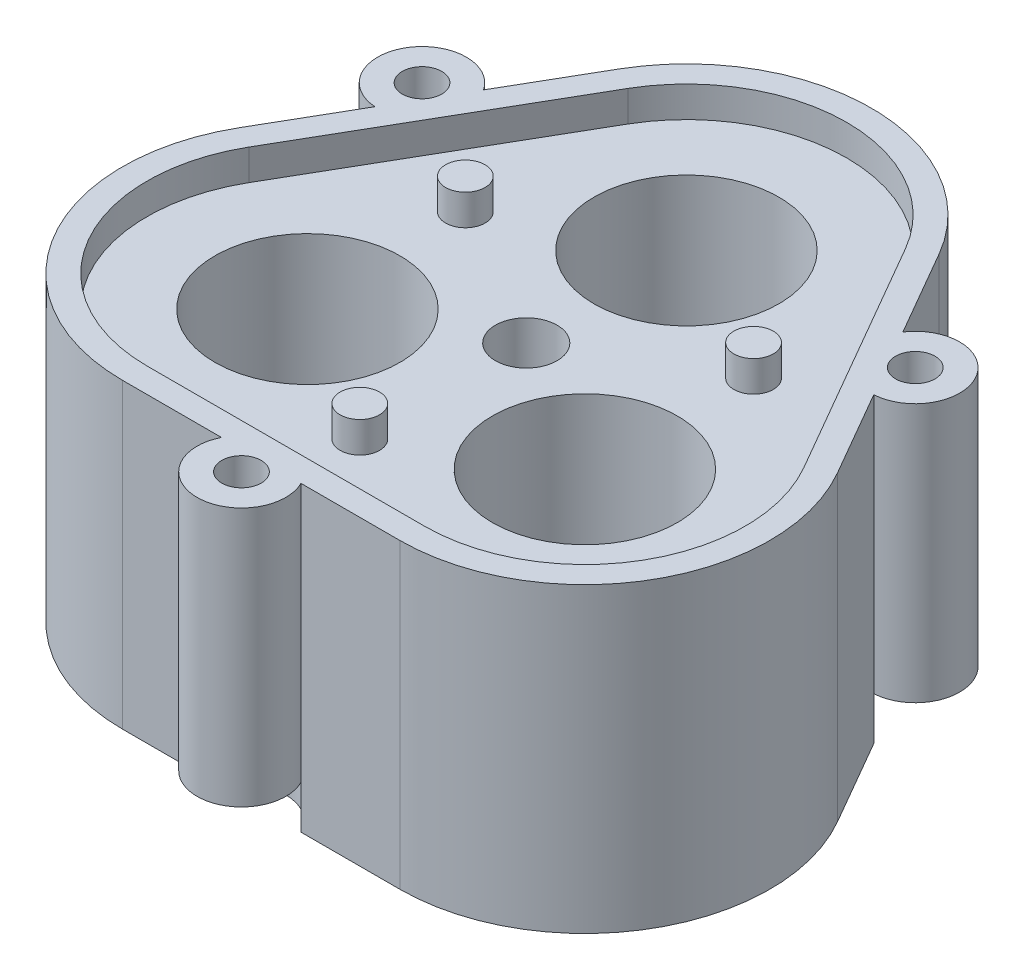
SolidWorks part; units mm, degrees
ref_plane "Front Plane" through (0, 0, 0) normal (0, 0, 1) x (1, 0, 0)
ref_plane "Top Plane" through (0, 0, 0) normal (0, 1, 0) x (1, 0, 0)
ref_plane "Right Plane" through (0, 0, 0) normal (1, 0, 0) x (0, 0, -1)
sketch "Sketch2" plane through (0, 0, 0) normal (0, 1, 0) x (1, 0, 0)
  line L0 (0, 0) -> (0, 12.9904) construction
  line L1 (0, 0) -> (11.25, -6.4952) construction
  line L2 (0, 0) -> (-11.25, -6.4952) construction
  line L3 (0, 12.9904) -> (-11.25, -6.4952) construction
  line L4 (-11.25, -6.4952) -> (11.25, -6.4952) construction
  line L5 (-11.25, -13.9952) -> (11.25, -13.9952) construction
  line L6 (6.4952, 16.7404) -> (17.7452, -2.7452) construction
  line L7 (-6.4952, 16.7404) -> (-17.7452, -2.7452) construction
  line L8 (-37.2308, -21.4952) -> (37.2308, -21.4952)
  line L9 (0, 42.9904) -> (-37.2308, -21.4952)
  line L10 (0, 42.9904) -> (37.2308, -21.4952)
  circle A0 centre (0, 12.9904) radius 7.5
  circle A1 centre (-11.25, -6.4952) radius 7.5
  circle A2 centre (11.25, -6.4952) radius 7.5
  circle A3 centre (0, 0) radius 2.5
  circle A4 centre (-11.25, -6.4952) radius 15 construction
  dimension "D3" = 15
  dimension "D9" = 5
  dimension "D10" = 30
  dimension "D1" = 120
  dimension "D2" = 120
  dimension "D4" = 22.5
  dimension "D5" = 7.5
  dimension "D6" = 7.5
  dimension "D7" = 7.5
  dimension "D8" = 74.4615
extrude "Boss-Extrude1" add sketch "Sketch2" along normal blind 12
sketch "Sketch4" plane through (0, 0, 0) normal (0, -1, 0) x (1, 0, 0)
  line L0 (-37.2308, 21.4952) -> (37.2308, 21.4952)
  line L1 (37.2308, 21.4952) -> (0, -42.9904)
  line L2 (0, -42.9904) -> (-37.2308, 21.4952)
  circle A0 centre (-11.25, 6.4952) radius 6
  circle A1 centre (11.25, 6.4952) radius 6
  circle A2 centre (0, -12.9904) radius 6
  circle A3 centre (0, 0) radius 2.5
  dimension "D1" = 12
  dimension "D2" = 5
extrude "Boss-Extrude2" add sketch "Sketch4" along normal blind 8
ref_plane "Plane1" through (0, -8, 0) normal (0, 1, 0) x (1, 0, 0)
sketch "Sketch7" plane through (0, -8, 0) normal (0, 1, 0) x (1, 0, 0)
  circle A0 centre (0, 12.9904) radius 4
  circle A1 centre (-11.25, -6.4952) radius 4
  circle A2 centre (11.25, -6.4952) radius 4
  dimension "D1" = 8
extrude "Boss-Extrude3" add sketch "Sketch7" along normal blind 8 separate body
sketch "Sketch9" plane through (0, -8, 0) normal (0, 1, 0) x (1, 0, 0)
  line L0 (0, 42.9904) -> (-37.2308, -21.4952)
  line L1 (-37.2308, -21.4952) -> (37.2308, -21.4952)
  line L2 (37.2308, -21.4952) -> (0, 42.9904)
extrude "Boss-Extrude4" add sketch "Sketch9" against normal blind 2
sketch "Sketch10" plane through (0, -8, 0) normal (0, 1, 0) x (1, 0, 0)
  line L0 (0, 0) -> (-11.25, -6.4952) construction
  line L1 (-11.25, -6.4952) -> (0, 12.9904) construction
  line L2 (0, 12.9904) -> (0, 0) construction
  line L3 (0, 0) -> (11.25, -6.4952) construction
  line L4 (11.25, -6.4952) -> (0, 12.9904) construction
  line L5 (-11.25, -6.4952) -> (11.25, -6.4952) construction
  line L6 (-11.25, -6.4952) -> (-12.6686, -1.7007) construction
  line L7 (-11.25, -6.4952) -> (-8.386, -2.3967) construction
  line L8 (-11.25, -6.4952) -> (-6.26, -6.179) construction
  line L9 (-11.25, -6.4952) -> (-7.8916, -10.1994) construction
  line L10 (-11.25, -6.4952) -> (-12.0521, -11.4304) construction
  line L11 (-11.25, -6.4952) -> (-15.6086, -8.9451) construction
  line L12 (-11.25, -6.4952) -> (-15.883, -4.615) construction
  line L13 (0, 12.9904) -> (4.8615, 11.8217) construction
  line L14 (0, 12.9904) -> (2.1174, 8.4608) construction
  line L15 (0, 12.9904) -> (-2.2212, 8.5108) construction
  line L16 (0, 12.9904) -> (-4.8871, 11.934) construction
  line L17 (0, 12.9904) -> (-3.873, 16.1527) construction
  line L18 (0, 12.9904) -> (0.0576, 17.99) construction
  line L19 (0, 12.9904) -> (3.9448, 16.0626) construction
  line L20 (11.25, -6.4952) -> (7.8071, -10.121) construction
  line L21 (11.25, -6.4952) -> (6.2686, -6.0641) construction
  line L22 (11.25, -6.4952) -> (8.4812, -2.3318) construction
  line L23 (11.25, -6.4952) -> (12.7787, -1.7346) construction
  line L24 (11.25, -6.4952) -> (15.9251, -4.7222) construction
  line L25 (11.25, -6.4952) -> (15.551, -9.0449) construction
  line L26 (11.25, -6.4952) -> (11.9382, -11.4476) construction
  circle A1 centre (-8.386, -2.3967) radius 0.75
  circle A4 centre (-11.25, -6.4952) radius 4 construction
  circle A5 centre (-11.25, -6.4952) radius 6 construction
  circle A6 centre (-11.25, -6.4952) radius 5 construction
  circle A7 centre (-12.6686, -1.7007) radius 0.75
  circle A8 centre (-6.26, -6.179) radius 0.75
  circle A9 centre (-7.8916, -10.1994) radius 0.75
  circle A10 centre (-12.0521, -11.4304) radius 0.75
  circle A11 centre (-15.6086, -8.9451) radius 0.75
  circle A12 centre (-15.883, -4.615) radius 0.75
  circle A13 centre (2.1174, 8.4608) radius 0.75
  circle A14 centre (4.8615, 11.8217) radius 0.75
  circle A15 centre (-2.2212, 8.5108) radius 0.75
  circle A16 centre (-4.8871, 11.934) radius 0.75
  circle A17 centre (-3.873, 16.1527) radius 0.75
  circle A18 centre (0.0576, 17.99) radius 0.75
  circle A19 centre (3.9448, 16.0626) radius 0.75
  circle A20 centre (0, 12.9904) radius 4 construction
  circle A21 centre (0, 12.9904) radius 6 construction
  circle A22 centre (0, 12.9904) radius 5 construction
  circle A23 centre (6.2686, -6.0641) radius 0.75
  circle A24 centre (7.8071, -10.121) radius 0.75
  circle A25 centre (8.4812, -2.3318) radius 0.75
  circle A26 centre (12.7787, -1.7346) radius 0.75
  circle A27 centre (15.9251, -4.7222) radius 0.75
  circle A28 centre (15.551, -9.0449) radius 0.75
  circle A29 centre (11.9382, -11.4476) radius 0.75
  circle A30 centre (11.25, -6.4952) radius 4 construction
  circle A31 centre (11.25, -6.4952) radius 6 construction
  circle A32 centre (11.25, -6.4952) radius 5 construction
  circle A33 centre (0, 0) radius 2.5
  point P27 (-11.25, -6.4952)
  point P47 (0, 12.9904)
  point P66 (11.25, -6.4952)
  point P67 (0, 0)
  dimension "D1" = 12
  dimension "D2" = 8
  dimension "D3" = 10
  dimension "D4" = 1.5
  dimension "D7" = 5
  dimension "D5" = 7
  dimension "D6" = 3
extrude "Cut-Extrude2" cut sketch "Sketch10" against normal through all both and the other way through all
ref_plane "Plane2" through (0, 12, 0) normal (0, 1, 0) x (1, 0, 0)
sketch "Sketch12" plane through (0, 12, 0) normal (0, 1, 0) x (1, 0, 0)
  line L0 (-12.9904, 20.4904) -> (-24.2404, 1.0048)
  line L4 (-11.25, -21.4952) -> (11.25, -21.4952)
  line L7 (24.2404, 1.0048) -> (12.9904, 20.4904)
  arc A0 (12.9904, 20.4904) -> (-12.9904, 20.4904) centre (0, 12.9904) ccw
  arc A1 (-24.2404, 1.0048) -> (-11.25, -21.4952) centre (-11.25, -6.4952) ccw
  arc A2 (11.25, -21.4952) -> (24.2404, 1.0048) centre (11.25, -6.4952) ccw
  circle A3 centre (0, 0) radius 57.2843
extrude "Cut-Extrude3" cut sketch "Sketch12" against normal through all both and the other way through all
sketch "Sketch13" plane through (0, 12, 0) normal (0, 1, 0) x (1, 0, 0)
  line L0 (-11.2583, 19.4904) -> (-22.5083, 0.0048)
  line L1 (-11.25, -19.4952) -> (11.25, -19.4952)
  line L2 (11.2583, 19.4904) -> (22.5083, 0.0048)
  line L3 (-12.9904, 20.4904) -> (-24.2404, 1.0048) construction
  line L5 (-11.25, -21.4952) -> (11.25, -21.4952)
  line L6 (24.2404, 1.0048) -> (12.9904, 20.4904)
  line L7 (-12.9904, 20.4904) -> (-24.2404, 1.0048)
  line L8 (0.0166, -0.0096) -> (-16.8833, 9.7476) construction
  arc A1 (-22.5083, 0.0048) -> (-11.25, -19.4952) centre (-11.25, -6.4952) ccw
  arc A2 (-0.0166, -0.0096) -> (0.0166, -0.0096) centre (0, 12.9904) ccw
  arc A3 (11.25, -19.4952) -> (22.5083, 0.0048) centre (11.25, -6.4952) ccw
  arc A4 (0.0166, -0.0096) -> (0, 0.0192) centre (-11.25, -6.4952) ccw
  arc A5 (0, 0.0192) -> (-0.0166, -0.0096) centre (11.25, -6.4952) ccw
  arc A6 (11.2583, 19.4904) -> (-11.2583, 19.4904) centre (0, 12.9904) ccw
  arc A8 (11.25, -21.4952) -> (24.2404, 1.0048) centre (11.25, -6.4952) ccw
  arc A9 (12.9904, 20.4904) -> (-12.9904, 20.4904) centre (0, 12.9904) ccw
  arc A10 (-24.2404, 1.0048) -> (-11.25, -21.4952) centre (-11.25, -6.4952) ccw
  circle A11 centre (-11.6872, 6.7476) radius 1.6
  circle A12 centre (11.6872, 6.7476) radius 1.6
  circle A13 centre (0, -13.4952) radius 1.6
  point P42 (0, 0)
  dimension "D2" = 13
  dimension "D3" = 3.2
  dimension "D1" = 2
  dimension "D4" = 6
  dimension "D5" = 3
sketch "Sketch15" plane through (0, -8, 0) normal (0, 1, 0) x (1, 0, 0)
  circle A0 centre (0, 12.9904) radius 1.6
  circle A1 centre (-11.25, -6.4952) radius 1.6
  circle A2 centre (11.25, -6.4952) radius 1.6
  dimension "D1" = 3.2
extrude "Cut-Extrude4" cut sketch "Sketch15" against normal through all both and the other way through all
extrude "Boss-Extrude5" add sketch "Sketch13" along normal blind 2.5 contours L7 A10 L5 A8 L6 A9 A6 L2 A3 L1 A1 L0 | A13 | A12 | A11
ref_plane "Plane3" through (0, 14.5, 0) normal (0, 1, 0) x (1, 0, 0)
sketch "Sketch16" plane through (0, 14.5, 0) normal (0, 1, 0) x (1, 0, 0)
  line L0 (0, 0) -> (-40.8337, 23.5754) construction
  line L11 (-12.9904, 20.4904) -> (-24.2404, 1.0048) construction
  circle A6 centre (-20.001, 11.5476) radius 1.6
  circle A7 centre (-20.001, 11.5476) radius 3.6
  circle A8 centre (20.001, 11.5476) radius 1.6
  circle A9 centre (20.001, 11.5476) radius 3.6
  circle A10 centre (0, -23.0952) radius 1.6
  circle A11 centre (0, -23.0952) radius 3.6
  point P16 (0, 0)
  point P26 (1.0392, -1.8)
  dimension "D1" = 3.2
  dimension "D3" = 3
  dimension "D2" = 2
extrude "Boss-Extrude6" add sketch "Sketch16" against normal blind 21
ref_plane "Plane4" through (0, -10, 0) normal (0, 1, 0) x (1, 0, 0)
sketch "Sketch19" plane through (0, -10, 0) normal (0, 1, 0) x (1, 0, 0)
  circle A0 centre (20.001, 11.5476) radius 1.6
  circle A1 centre (20.001, 11.5476) radius 3.6
extrude "Cut-Extrude10" cut sketch "Sketch19" along normal up to surface (3.5 mm away) and the other way through all up to face at (20.0876, -6.5, -11.1976)
pattern_circular "CirPattern1" count 3 over 360 about axis through (0, 0, 0) along (0, 1, 0) of "Cut-Extrude10"
sketch "Sketch20" plane through (0, 14.5, 0) normal (0, 1, 0) x (1, 0, 0)
  line L6 (-11.2583, 19.4904) -> (-22.5083, 0.0048)
  line L7 (-11.25, -19.4952) -> (11.25, -19.4952)
  line L8 (22.5083, 0.0048) -> (11.2583, 19.4904)
  line L9 (-11.2583, 19.4904) -> (-22.5083, 0.0048)
  line L10 (-11.25, -19.4952) -> (11.25, -19.4952)
  line L11 (22.5083, 0.0048) -> (11.2583, 19.4904)
  circle A5 centre (0, 12.9904) radius 7.5
  arc A6 (11.2583, 19.4904) -> (-11.2583, 19.4904) centre (0, 12.9904) ccw
  arc A7 (-22.5083, 0.0048) -> (-11.25, -19.4952) centre (-11.25, -6.4952) ccw
  arc A8 (11.25, -19.4952) -> (22.5083, 0.0048) centre (11.25, -6.4952) ccw
  arc A9 (11.2583, 19.4904) -> (-11.2583, 19.4904) centre (0, 12.9904) ccw
  arc A10 (-22.5083, 0.0048) -> (-11.25, -19.4952) centre (-11.25, -6.4952) ccw
  arc A11 (11.25, -19.4952) -> (22.5083, 0.0048) centre (11.25, -6.4952) ccw
  circle A12 centre (0, 12.9904) radius 7.5
  circle A14 centre (-11.6872, 6.7476) radius 1.6
  circle A15 centre (-11.6872, 6.7476) radius 1.6
  circle A17 centre (11.6872, 6.7476) radius 1.6
  circle A18 centre (11.6872, 6.7476) radius 1.6
  circle A25 centre (0, -13.4952) radius 1.6
  circle A26 centre (0, -13.4952) radius 1.6
  circle A28 centre (-11.25, -6.4952) radius 7.5
  circle A29 centre (-11.25, -6.4952) radius 7.5
  circle A31 centre (11.25, -6.4952) radius 7.5
  circle A32 centre (11.25, -6.4952) radius 7.5
  dimension "D1" = 0
  dimension "D2" = 0
  dimension "D3" = 0
  dimension "D4" = 0
  dimension "D5" = 0
  dimension "D6" = 0
  dimension "D7" = 0
